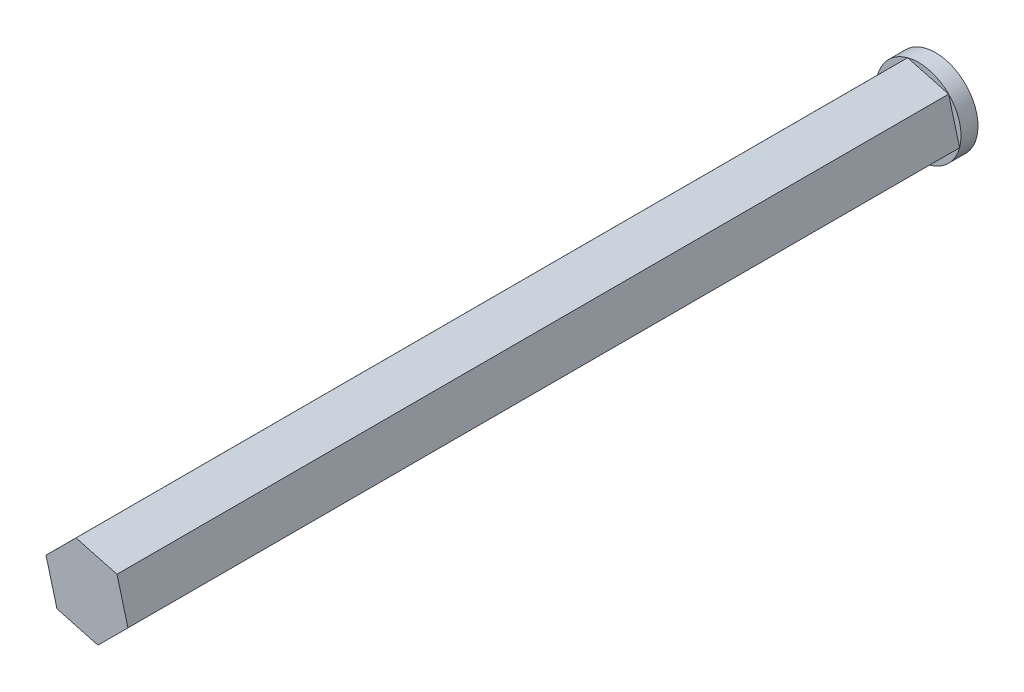
SolidWorks part; units mm, degrees
ref_plane "Alzado" through (0, 0, 0) normal (0, 0, 1) x (1, 0, 0)
ref_plane "Planta" through (0, 0, 0) normal (0, 1, 0) x (1, 0, 0)
ref_plane "Vista lateral" through (0, 0, 0) normal (1, 0, 0) x (0, 0, -1)
sketch "Croquis1" plane through (0, 0, 0) normal (0, 0, 1) x (1, 0, 0)
  circle A0 centre (-3.4657, 4.4773) radius 2.5
  dimension "D1" = 5
extrude "Saliente-Extruir2" add sketch "Croquis1" along normal blind 1 contours A0
sketch "Croquis2" plane through (0, 0, 1) normal (0, 0, 1) x (1, 0, 0)
  line L1 (-1.0513, 3.8288) -> (-1.6969, 6.244)
  line L2 (-1.6969, 6.244) -> (-4.1113, 6.8925)
  line L3 (-4.1113, 6.8925) -> (-5.8801, 5.1258)
  line L4 (-5.8801, 5.1258) -> (-5.2345, 2.7106)
  line L5 (-5.2345, 2.7106) -> (-2.8201, 2.0621)
  line L6 (-2.8201, 2.0621) -> (-1.0513, 3.8288)
  circle A0 centre (-3.4657, 4.4773) radius 2.1651 construction
  circle A1 centre (-3.4657, 4.4773) radius 2.5 construction
  dimension "D1" = 5
extrude "Saliente-Extruir3" add sketch "Croquis2" along normal blind 49
